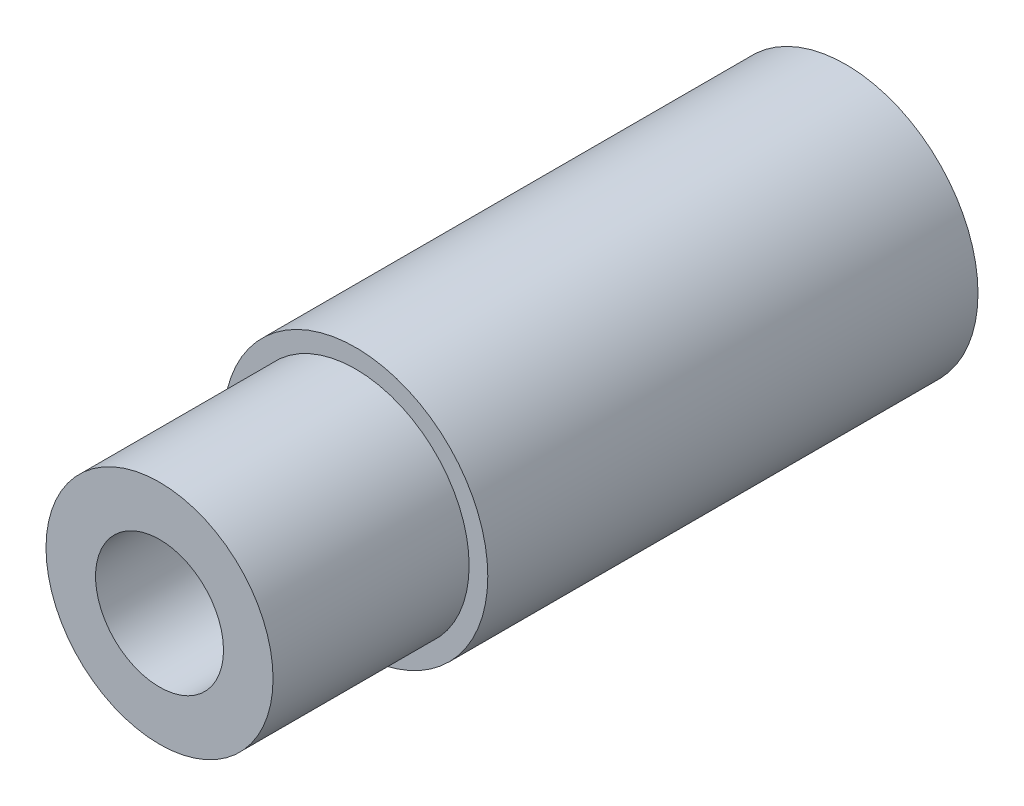
SolidWorks part; units mm, degrees
ref_plane "Front Plane" through (0, 0, 0) normal (0, 0, 1) x (1, 0, 0)
ref_plane "Top Plane" through (0, 0, 0) normal (0, 1, 0) x (1, 0, 0)
ref_plane "Right Plane" through (0, 0, 0) normal (1, 0, 0) x (0, 0, -1)
sketch "Sketch1" plane through (0, 0, 0) normal (0, 0, 1) x (1, 0, 0)
  circle A0 centre (0, 0) radius 3.2537
  circle A1 centre (0, 0) radius 1.5748
  dimension "D1" = 6.5075
  dimension "D2" = 3.1496
extrude "Boss-Extrude1" add sketch "Sketch1" along normal blind 12.065
sketch "Sketch2" plane through (0, 0, 12.065) normal (0, 0, 1) x (1, 0, 0)
  circle A0 centre (0, 0) radius 1.5748 construction
  circle A1 centre (0, 0) radius 1.5748
  circle A2 centre (0, 0) radius 2.794
  dimension "D1" = 5.588
extrude "Boss-Extrude2" add sketch "Sketch2" along normal blind 4.826
